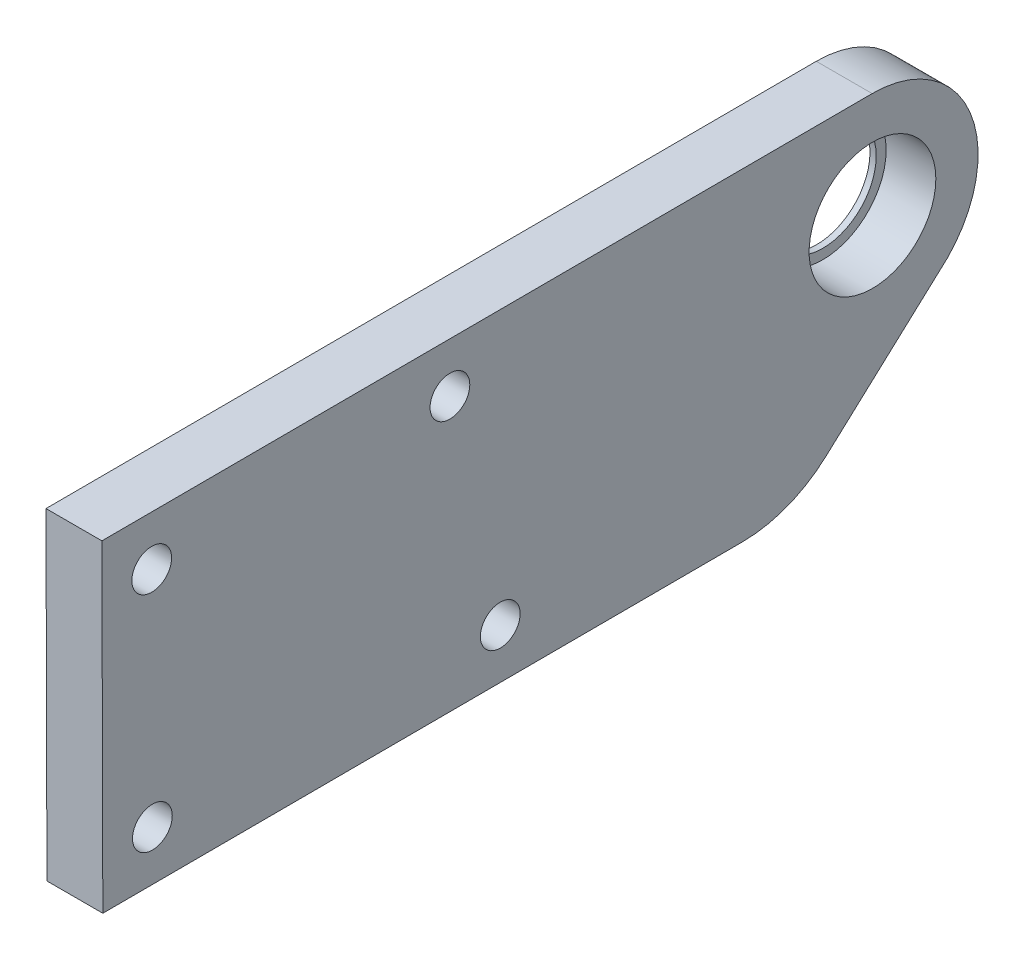
SolidWorks part; units mm, degrees
ref_plane "前视基准面" through (0, 0, 0) normal (0, 0, 1) x (1, 0, 0)
ref_plane "上视基准面" through (0, 0, 0) normal (0, 1, 0) x (1, 0, 0)
ref_plane "右视基准面" through (0, 0, 0) normal (1, 0, 0) x (0, 0, -1)
sketch "草图1" plane through (0, 0, 0) normal (1, 0, 0) x (0, 0, -1)
  line L47 (-61.9107, -17.7849) -> (-10.4109, -17.6369)
  line L48 (-3.6943, -15.0194) -> (6.0537, -6.1126)
  line L49 (-61.9854, 8.215) -> (-61.9107, -17.7849)
  line L50 (-61.9854, 8.215) -> (0.0144, 8.3932)
  circle A0 centre (0.0388, -0.1068) radius 4.3
  circle A166 centre (-57.9739, 4.2265) radius 1.6
  arc A169 (6.0537, -6.1126) -> (0.0144, 8.3932) centre (0.0388, -0.1068) ccw
  circle A170 centre (-29.9223, -13.6929) radius 1.6
  circle A171 centre (-33.974, 4.2955) radius 1.6
  circle A175 centre (-57.9222, -13.7734) radius 1.6
  arc A176 (-10.4109, -17.6369) -> (-3.6943, -15.0194) centre (-10.4396, -7.6369) ccw
  point P0 (-150, 0)
  point P1 (135, 0)
  point P9 (-344.9533, 138.7825)
  point P10 (187.1329, 101.1747)
  point P11 (165.9429, -19)
  point P12 (-156.9154, -19)
  dimension "D7" = 4
  dimension "D8" = 22
  dimension "D10" = 8.5
  dimension "D4" = 4
  dimension "D11" = 62
  dimension "D13" = 26
  dimension "D14" = 8.6
  dimension "D6" = 28
  dimension "D5" = 4
  dimension "D2" = 18
  dimension "D1" = 24
  dimension "D3" = 4
extrude "凸台-拉伸1" add sketch "草图1" along normal blind 4.5
sketch "草图2" plane through (4.5, 0, 0) normal (1, 0, 0) x (0, 0, -1)
  circle A0 centre (0.0388, -0.1068) radius 5.1
  dimension "D1" = 10.2
extrude "切除-拉伸1" cut sketch "草图2" against normal blind 4
